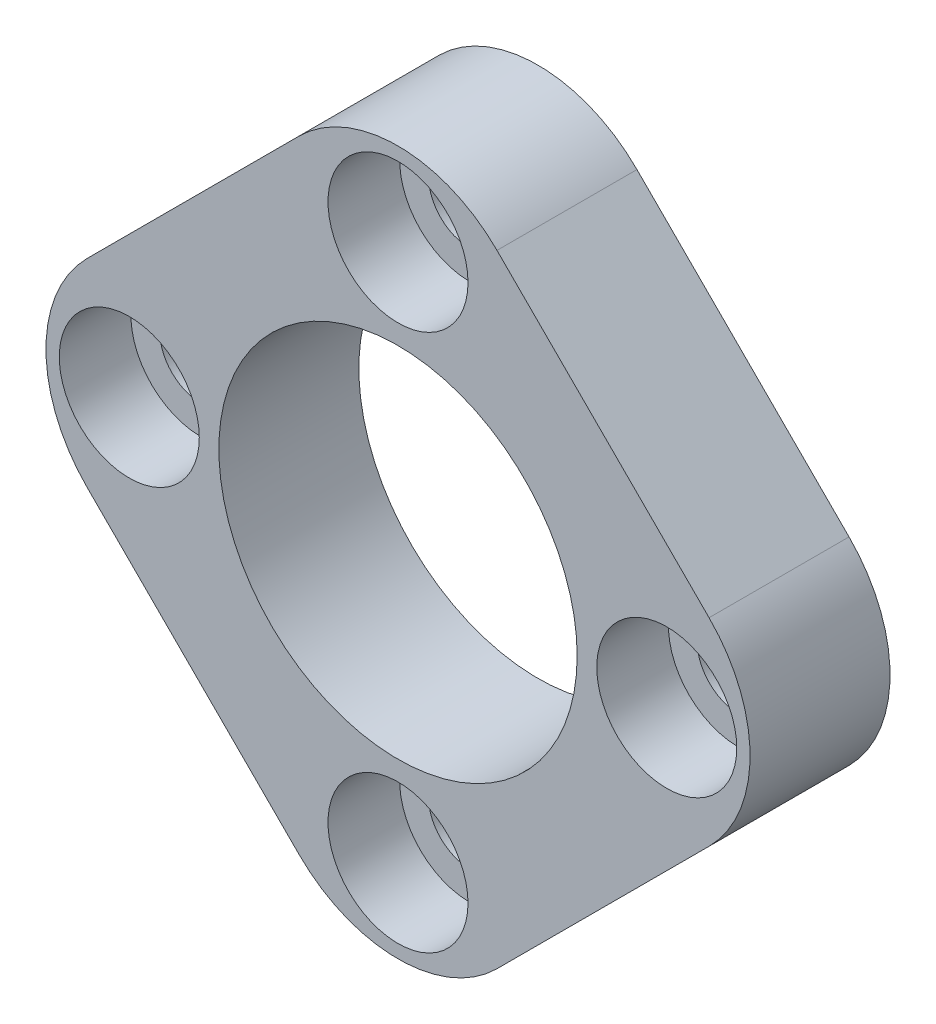
SolidWorks part; units mm, degrees
material "6061-T6 Al"
ref_plane "Front Plane" through (0, 0, 0) normal (0, 0, 1) x (1, 0, 0)
ref_plane "Top Plane" through (0, 0, 0) normal (0, 1, 0) x (1, 0, 0)
ref_plane "Right Plane" through (0, 0, 0) normal (1, 0, 0) x (0, 0, -1)
sketch "Sketch1" plane through (0, 0, 0) normal (0, 0, 1) x (1, 0, 0)
  line L0 (0, -16.2767) -> (-16.2767, 0)
  line L7 (0, -16.2767) -> (16.2767, 0)
  line L8 (-16.2767, 0) -> (0, 16.2767)
  line L9 (16.2767, 0) -> (0, 16.2767)
  line L10 (0, -16.2767) -> (0, 16.2767) construction
  line L11 (-16.2767, 0) -> (16.2767, 0) construction
  point P1 (0, 0)
  dimension "D1" = 23.0188
  dimension "D4" = 23.0188
extrude "Boss-Extrude1" add sketch "Sketch1" against normal blind 5.5562
sketch "Sketch2" plane through (0, 0, 0) normal (0, 0, 1) x (1, 0, 0)
  circle A0 centre (0, 0) radius 7.112
  dimension "D1" = 14.224
extrude "Cut-Extrude1" cut sketch "Sketch2" against normal through all
hole_wizard "CBORE for #4 Socket Head Cap Screw1" positions "Sketch4" profile "Sketch3" counterbore size "#4" standard "Ansi Inch" end condition through all
sketch "Sketch4" plane through (0, 0, 0) normal (0, 0, 1) x (1, 0, 0)
  point P0 (0, 10.668)
  dimension "D1" = 10.668
sketch "Sketch3" plane through (0, 10.668, 0) normal (1, 0, 0) x (0, -1, 0)
  line L0 (0, 0) -> (0, 5.5562)
  line L1 (0, 5.5562) -> (1.6319, 5.5562)
  line L3 (1.6319, 5.5562) -> (1.6319, 2.8448)
  line L4 (1.6319, 2.8448) -> (2.7788, 2.8448)
  line L5 (2.7788, 2.8448) -> (2.7788, 0)
  line L7 (2.7788, 0) -> (0, 0)
  line L11 (0, -6.35) -> (0, 107.95) construction
  dimension "Thru Hole Dia." = 3.2639
  dimension "Thru Hole Depth" = 5.5562
  dimension "C'Bore Dia." = 5.5575
  dimension "C'Bore Depth" = 2.8448
pattern_circular "CirPattern1" count 4 every 90 about axis through (0, 0, 0) along (0, 0, 1) of "CBORE for #4 Socket Head Cap Screw1"
fillet "Fillet1" radius 5.5562 4 edges at (-16.2767, 0, -2.7781) (0, -16.2767, -2.7781) (16.2767, 0, -2.7781) (0, 16.2767, -2.7781)
